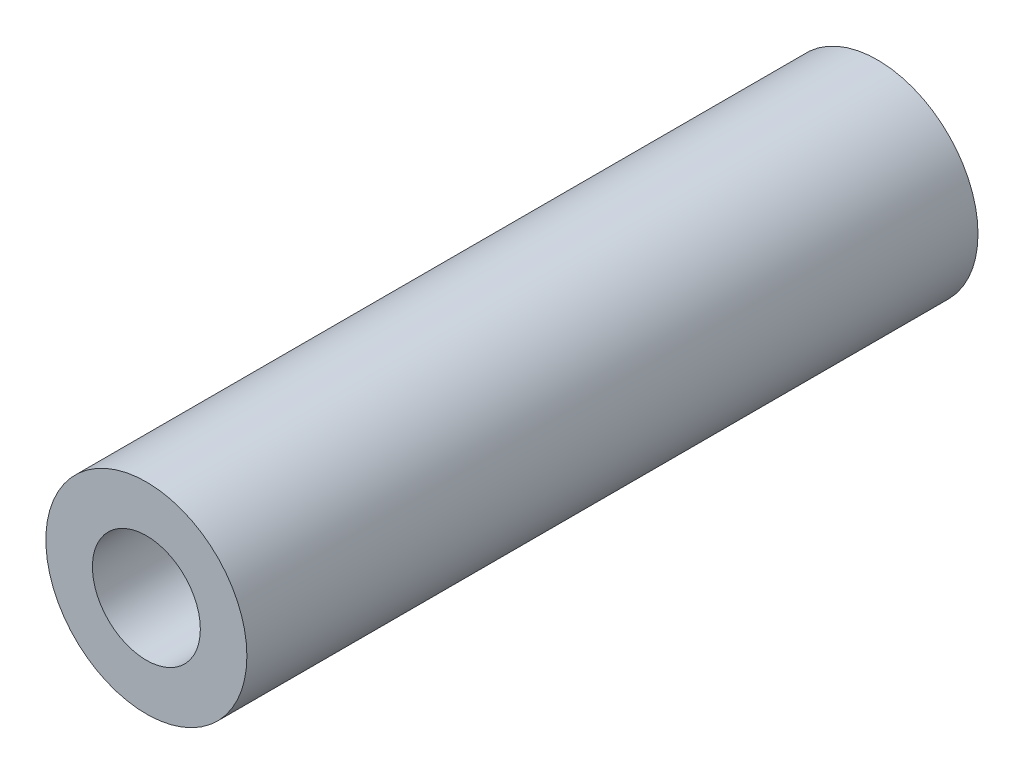
SolidWorks part; units mm, degrees
ref_plane "Front Plane" through (0, 0, 0) normal (0, 0, 1) x (1, 0, 0)
ref_plane "Top Plane" through (0, 0, 0) normal (0, 1, 0) x (1, 0, 0)
ref_plane "Right Plane" through (0, 0, 0) normal (1, 0, 0) x (0, 0, -1)
sketch "Sketch1" plane through (0, 0, 0) normal (0, 0, 1) x (1, 0, 0)
  circle A0 centre (0, 0) radius 1.5
  circle A1 centre (0, 0) radius 2.794
  dimension "D1" = 3
  dimension "D2" = 5.588
extrude "Boss-Extrude1" add sketch "Sketch1" along normal blind 20.32
